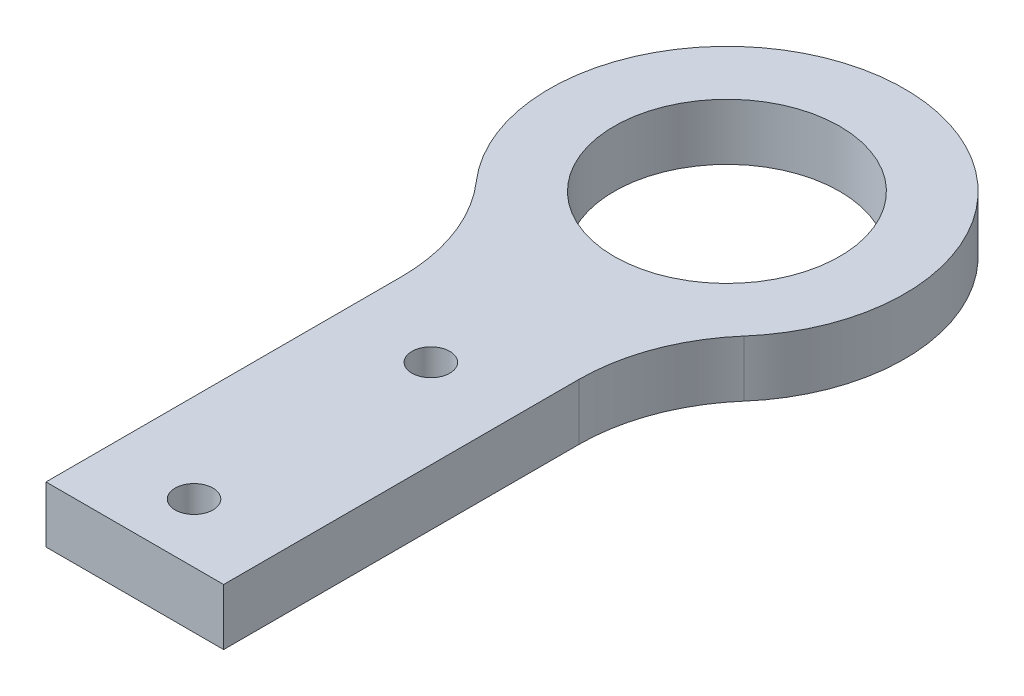
SolidWorks part; units mm, degrees
ref_plane "Front Plane" through (0, 0, 0) normal (0, 0, 1) x (1, 0, 0)
ref_plane "Top Plane" through (0, 0, 0) normal (0, 1, 0) x (1, 0, 0)
ref_plane "Right Plane" through (0, 0, 0) normal (1, 0, 0) x (0, 0, -1)
sketch "Sketch1" plane through (0, 0, 0) normal (0, 1, 0) x (1, 0, 0)
  line L0 (0, 0) -> (0, 50) construction
  line L1 (-7.5, 0) -> (7.5, 0)
  line L2 (7.5, 0) -> (7.5, 30)
  line L3 (-7.5, 30) -> (-7.5, 0)
  arc A0 (7.5, 30) -> (11.3014, 40.137) centre (22.9167, 30) cw
  arc A1 (11.3014, 40.137) -> (-11.3014, 40.137) centre (0, 50) ccw
  arc A2 (-11.3014, 40.137) -> (-7.5, 30) centre (-22.9167, 30) cw
  circle A3 centre (0, 50) radius 9.525
  circle A4 centre (0, 5) radius 1.6
  circle A5 centre (0, 25) radius 1.6
  dimension "D2" = 15
  dimension "D3" = 19.05
  dimension "D6" = 3.2
  dimension "D1" = 15
  dimension "D4" = 50
  dimension "D5" = 30
  dimension "D7" = 5
  dimension "D8" = 20
extrude "Boss-Extrude2" add sketch "Sketch1" along normal blind 4.7625
